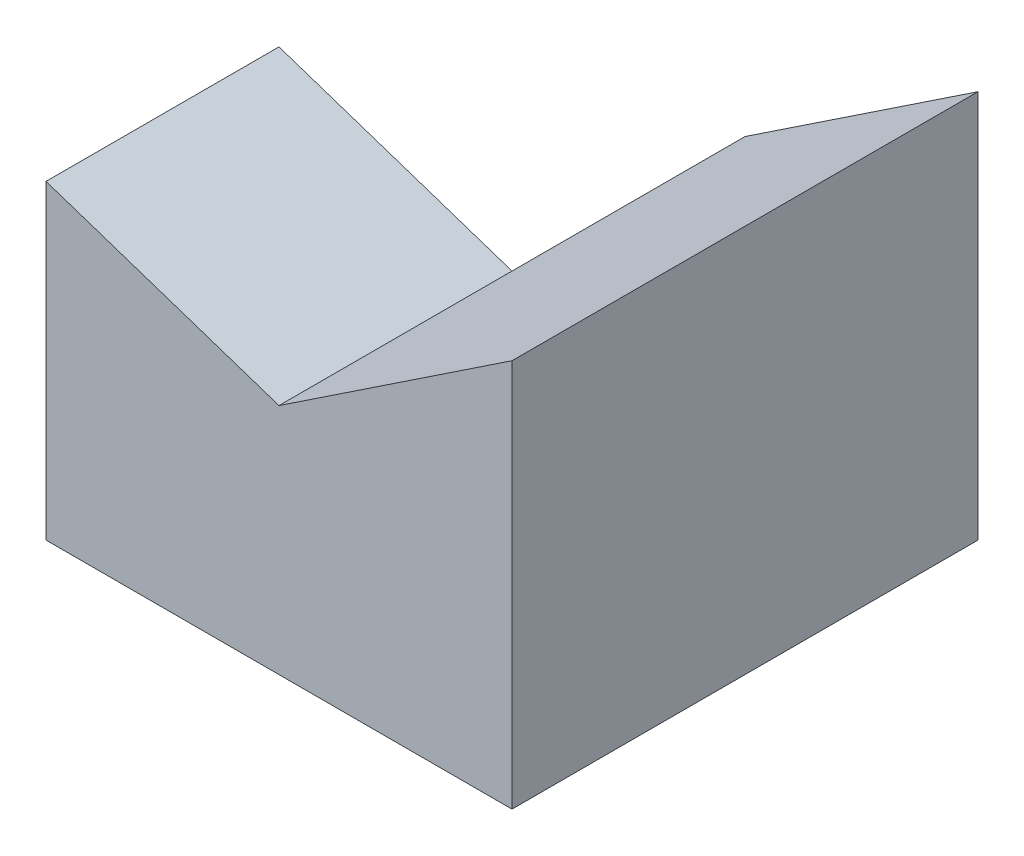
SolidWorks part; units mm, degrees
ref_plane "Front" through (0, 0, 0) normal (0, 0, 1) x (1, 0, 0)
ref_plane "Top" through (0, 0, 0) normal (0, 1, 0) x (1, 0, 0)
ref_plane "Right" through (0, 0, 0) normal (1, 0, 0) x (0, 0, -1)
sketch "Sketch1" plane through (0, 0, 0) normal (0, 1, 0) x (1, 0, 0)
  line L1 (-3, -3) -> (3, -3)
  line L2 (-3, -3) -> (-3, 3)
  line L3 (-3, 3) -> (3, 3)
  line L4 (3, -3) -> (3, 3)
  line L5 (-3, -3) -> (3, 3) construction
  line L6 (-3, 3) -> (3, -3) construction
  point P0 (0, 0)
  dimension "D1" = 6
  dimension "D2" = 6
extrude "Boss-Extrude1" add sketch "Sketch1" along normal blind 5
sketch "Sketch5" plane through (0, 0, 3) normal (0, 0, 1) x (1, 0, 0)
  line L0 (-3, 5) -> (0, 3)
  line L1 (0, 3) -> (3, 5)
  line L2 (0, 3) -> (-3, 4)
  line L6 (-3, 0) -> (3, 0)
  line L7 (3, 0) -> (3, 5)
  line L8 (3, 5) -> (-3, 5)
  line L9 (-3, 5) -> (-3, 0)
  line L10 (-3, 0) -> (3, 0)
  line L11 (3, 0) -> (3, 5)
  line L12 (3, 5) -> (-3, 5)
  line L13 (-3, 5) -> (-3, 0)
  line M7 (3, 5) -> (-3, 5)
  line M8 (-3, 5) -> (-3, 0)
  dimension "D2" = 3
  dimension "D3" = 1
  dimension "D1" = 0
extrude "Cut-Extrude3" cut sketch "Sketch5" against normal blind 13.5 contours L0 L1 M7 | L2 L0 M8
sketch "Sketch7" plane through (0, 0, -3) normal (0, 0, -1) x (-1, 0, 0)
  line L0 (0, 3) -> (3, 0)
  line L1 (3, 0) -> (3, 6)
  line L2 (3, 6) -> (0, 3)
extrude "Cut-Extrude4" cut sketch "Sketch7" against normal blind 3
